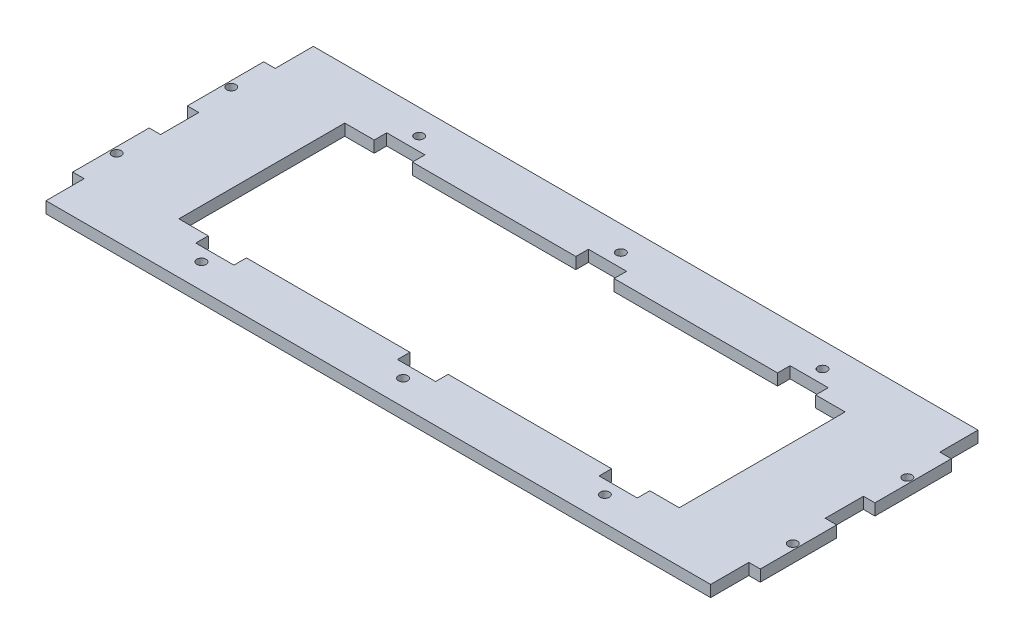
SolidWorks part; units mm, degrees
material "Acrylic (Medium-high impact)"
ref_plane "Front" through (0, 0, 0) normal (0, 0, 1) x (1, 0, 0)
ref_plane "Top" through (0, 0, 0) normal (0, 1, 0) x (1, 0, 0)
ref_plane "Right" through (0, 0, 0) normal (1, 0, 0) x (0, 0, -1)
sketch "Sketch1" plane through (0, 0, 0) normal (0, 1, 0) x (1, 0, 0)
  line L0 (-110.49, 0) -> (110.49, 0) construction
  line L1 (-110.49, -44.45) -> (110.49, -44.45)
  line L3 (-110.49, 44.45) -> (110.49, 44.45)
  line L4 (114.3, -31.75) -> (114.3, -6.35)
  line L5 (110.49, -44.45) -> (110.49, -31.75)
  line L6 (110.49, -31.75) -> (114.3, -31.75)
  line L7 (0, 44.45) -> (0, -44.45) construction
  line L8 (114.3, -6.35) -> (110.49, -6.35)
  line L9 (110.49, -6.35) -> (110.49, 6.35)
  line L10 (110.49, 6.35) -> (114.3, 6.35)
  line L11 (114.3, 31.75) -> (110.49, 31.75)
  line L12 (110.49, 31.75) -> (110.49, 44.45)
  line L13 (114.3, 6.35) -> (114.3, 31.75)
  line L14 (-114.3, 6.35) -> (-114.3, 31.75)
  line L15 (-110.49, 31.75) -> (-110.49, 44.45)
  line L16 (-114.3, 31.75) -> (-110.49, 31.75)
  line L17 (-110.49, 6.35) -> (-114.3, 6.35)
  line L18 (-110.49, -6.35) -> (-110.49, 6.35)
  line L19 (-114.3, -6.35) -> (-110.49, -6.35)
  line L20 (-110.49, -31.75) -> (-114.3, -31.75)
  line L21 (-110.49, -44.45) -> (-110.49, -31.75)
  line L22 (-114.3, -31.75) -> (-114.3, -6.35)
  line L24 (112.395, 31.75) -> (112.395, 6.35) construction
  line L32 (-83.185, -27.5844) -> (-73.406, -27.5844)
  line L33 (-73.406, -27.5844) -> (-73.406, -31.75)
  line L34 (-73.406, -31.75) -> (-60.706, -31.75)
  line L35 (-60.706, -31.75) -> (-60.706, -27.5844)
  line L36 (-60.706, -27.5844) -> (-6.35, -27.5844)
  line L37 (-6.35, -27.5844) -> (-6.35, -31.75)
  line L38 (-6.35, -31.75) -> (6.35, -31.75)
  line L39 (6.35, -31.75) -> (6.35, -27.5844)
  line L40 (6.35, -27.5844) -> (60.706, -27.5844)
  line L41 (60.706, -27.5844) -> (60.706, -31.75)
  line L42 (60.706, -31.75) -> (73.406, -31.75)
  line L43 (73.406, -31.75) -> (73.406, -27.5844)
  line L44 (73.406, -27.5844) -> (83.185, -27.5844)
  line L45 (83.185, -27.5844) -> (83.185, 27.5844)
  line L46 (83.185, 27.5844) -> (73.406, 27.5844)
  line L47 (73.406, 27.5844) -> (73.406, 31.75)
  line L48 (73.406, 31.75) -> (60.706, 31.75)
  line L49 (60.706, 31.75) -> (60.706, 27.5844)
  line L50 (60.706, 27.5844) -> (6.35, 27.5844)
  line L51 (6.35, 27.5844) -> (6.35, 31.75)
  line L52 (6.35, 31.75) -> (-6.35, 31.75)
  line L53 (-6.35, 31.75) -> (-6.35, 27.5844)
  line L54 (-6.35, 27.5844) -> (-60.706, 27.5844)
  line L55 (-60.706, 27.5844) -> (-60.706, 31.75)
  line L56 (-60.706, 31.75) -> (-73.406, 31.75)
  line L57 (-73.406, 31.75) -> (-73.406, 27.5844)
  line L58 (-73.406, 27.5844) -> (-83.185, 27.5844)
  line L59 (-83.185, 27.5844) -> (-83.185, -27.5844)
  line L60 (-67.056, -31.75) -> (-67.056, -44.45) construction
  circle A0 centre (112.395, 19.05) radius 1.524
  circle A1 centre (-112.395, 19.05) radius 1.524
  circle A2 centre (-112.395, -19.05) radius 1.524
  circle A3 centre (112.395, -19.05) radius 1.524
  circle A4 centre (-67.056, -36.195) radius 1.524
  circle A5 centre (0, -36.195) radius 1.524
  circle A6 centre (67.056, -36.195) radius 1.524
  circle A7 centre (67.056, 36.195) radius 1.524
  circle A8 centre (-67.056, 36.195) radius 1.524
  circle A9 centre (0, 36.195) radius 1.524
  point P0 (0, 0)
  point P10 (0, 0)
  point P20 (110.49, 0)
  point P71 (-83.185, 0)
  point P73 (0, 31.75)
  point P82 (17.0815, 36.195)
  dimension "D5" = 3.048
  dimension "D6" = 55.1688
  dimension "D1" = 228.6
  dimension "D2" = 88.9
  dimension "D3" = 3.81
  dimension "D4" = 25.4
  dimension "D7" = 12.7
  dimension "D8" = 63.5
  dimension "D9" = 166.37
  dimension "D10" = 54.356
  dimension "D12" = 72.39
  dimension "D11" = 3
extrude "Boss-Extrude1" add sketch "Sketch1" along normal blind 3.81
